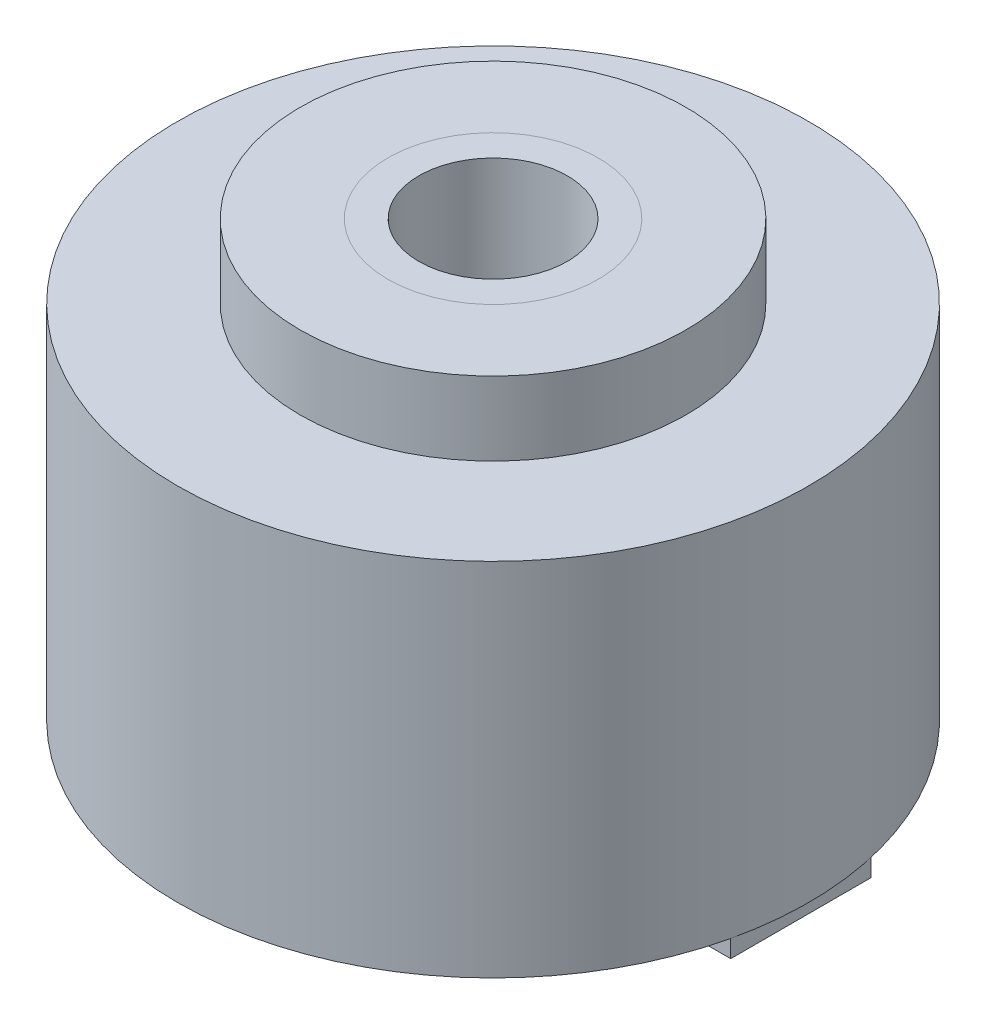
SolidWorks part; units mm, degrees
ref_plane "Front Plane" through (0, 0, 0) normal (0, 0, 1) x (1, 0, 0)
ref_plane "Top Plane" through (0, 0, 0) normal (0, 1, 0) x (1, 0, 0)
ref_plane "Right Plane" through (0, 0, 0) normal (1, 0, 0) x (0, 0, -1)
sketch "Sketch2" plane through (0, 0, 0) normal (0, 1, 0) x (1, 0, 0)
  circle A0 centre (0, 0) radius 6.35
  circle A1 centre (0, 0) radius 27
  dimension "D1" = 54
  dimension "D2" = 12.7
extrude "Boss-Extrude1" add sketch "Sketch2" along normal blind 30.861
sketch "Sketch3" plane through (0, 30.861, 0) normal (0, 1, 0) x (1, 0, 0)
  circle A0 centre (0, 0) radius 16.5
  circle A1 centre (0, 0) radius 9
  dimension "D1" = 18
  dimension "D2" = 33
extrude "Boss-Extrude2" add sketch "Sketch3" along normal blind 6.3
sketch "Sketch4" plane through (0, 30.861, 0) normal (0, 1, 0) x (1, 0, 0)
  circle A0 centre (0, 0) radius 9
extrude "Boss-Extrude3" add sketch "Sketch4" along normal up to surface (6.3 mm away) and the other way offset from surface (31.861 mm away) 1 separate body contours A0 up to face at (0, 37.161, 16.5) other way up to face at (0, 0, 27)
sketch "Sketch5" plane through (0, 37.161, 0) normal (0, 1, 0) x (1, 0, 0)
  circle A0 centre (0, 0) radius 6.35
  dimension "D1" = 12.7
extrude "Cut-Extrude1" cut sketch "Sketch5" against normal through all
sketch "Sketch6" plane through (0, 0, 0) normal (0, -1, 0) x (1, 0, 0)
  line L0 (33.0285, 0) -> (-33.9645, 0) construction
  line L1 (26.3249, -6) -> (26.3249, 6)
  line L2 (26.3249, 6) -> (9.1799, 6)
  line L3 (9.1799, 6) -> (9.1799, 3)
  line L4 (9.1799, -6) -> (9.1799, -3)
  line L5 (26.3249, -6) -> (9.1799, -6)
  circle A0 centre (0, 0) radius 27 construction
  arc A1 (9.1799, 3) -> (9.1799, -3) centre (9.1799, 0) cw
  point P17 (26.3249, 0)
  dimension "D2" = 3
  dimension "D1" = 6
  dimension "D3" = 17.145
extrude "Boss-Extrude4" add sketch "Sketch6" along normal blind 1.5 separate body
